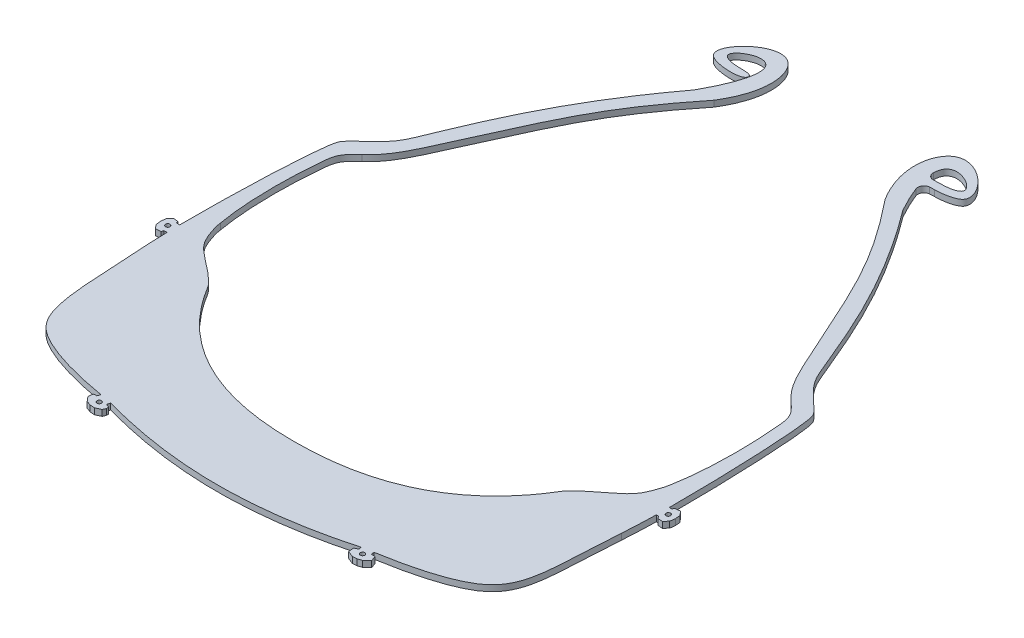
SolidWorks part; units mm, degrees
ref_plane "Front Plane" through (0, 0, 0) normal (0, 0, 1) x (1, 0, 0)
ref_plane "Top Plane" through (0, 0, 0) normal (0, 1, 0) x (1, 0, 0)
ref_plane "Right Plane" through (0, 0, 0) normal (1, 0, 0) x (0, 0, -1)
sketch "Sketch1" plane through (0, 0, 0) normal (0, 1, 0) x (1, 0, 0)
  line L0 (-56.7342, 4649.685) -> (-54.3432, 4649.8666)
  line L1 (-54.3432, 4649.8666) -> (-51.9673, 4650.1279)
  line L2 (-51.9673, 4650.1279) -> (-49.6128, 4650.4904)
  line L3 (-49.6128, 4650.4904) -> (-47.2873, 4650.9763)
  line L4 (-47.2873, 4650.9763) -> (-45.0028, 4651.606)
  line L5 (-45.0028, 4651.606) -> (-42.7754, 4652.393)
  line L6 (-42.7754, 4652.393) -> (-40.6236, 4653.3398)
  line L7 (-40.6236, 4653.3398) -> (-38.5569, 4654.4471)
  line L8 (-38.5569, 4654.4471) -> (-36.5628, 4655.7048)
  line L9 (-36.5628, 4655.7048) -> (-34.628, 4657.0886)
  line L10 (-34.628, 4657.0886) -> (-32.7572, 4658.5809)
  line L11 (-32.7572, 4658.5809) -> (-31.8781, 4659.3559)
  line L12 (-31.8781, 4659.3559) -> (-31.0378, 4660.1663)
  line L13 (-31.0378, 4660.1663) -> (-30.2434, 4661.0133)
  line L14 (-30.2434, 4661.0133) -> (-29.4929, 4661.8977)
  line L15 (-29.4929, 4661.8977) -> (-28.0377, 4663.8002)
  line L16 (-28.0377, 4663.8002) -> (-26.6418, 4665.7643)
  line L17 (-26.6418, 4665.7643) -> (-25.2842, 4667.7433)
  line L18 (-25.2842, 4667.7433) -> (-24.5616, 4668.7671)
  line L19 (-24.5616, 4668.7671) -> (-24.1207, 4669.3049)
  line L20 (-24.1207, 4669.3049) -> (-23.6287, 4669.8041)
  line L21 (-23.6287, 4669.8041) -> (-22.6527, 4670.6453)
  line L22 (-22.6527, 4670.6453) -> (-21.6624, 4671.4168)
  line L23 (-21.6624, 4671.4168) -> (-19.7154, 4672.8766)
  line L24 (-19.7154, 4672.8766) -> (-18.7888, 4673.6051)
  line L25 (-18.7888, 4673.6051) -> (-17.9151, 4674.3646)
  line L26 (-17.9151, 4674.3646) -> (-17.0961, 4675.1711)
  line L27 (-17.0961, 4675.1711) -> (-16.3332, 4676.0235)
  line L28 (-16.3332, 4676.0235) -> (-14.888, 4677.8872)
  line L29 (-14.888, 4677.8872) -> (-14.2651, 4678.8282)
  line L30 (-14.2651, 4678.8282) -> (-13.7395, 4679.8092)
  line L31 (-13.7395, 4679.8092) -> (-13.3157, 4680.8364)
  line L32 (-13.3157, 4680.8364) -> (-12.9921, 4681.9053)
  line L33 (-12.9921, 4681.9053) -> (-12.765, 4683.0137)
  line L34 (-12.765, 4683.0137) -> (-12.6116, 4684.156)
  line L35 (-12.6116, 4684.156) -> (-12.4221, 4686.5439)
  line L36 (-12.4221, 4686.5439) -> (-12.3049, 4688.9547)
  line L37 (-12.3049, 4688.9547) -> (-12.23, 4691.3606)
  line L38 (-12.23, 4691.3606) -> (-12.2173, 4693.7469)
  line L39 (-12.2173, 4693.7469) -> (-12.2979, 4696.128)
  line L40 (-12.2979, 4696.128) -> (-12.4621, 4698.525)
  line L41 (-12.4621, 4698.525) -> (-12.9016, 4703.3562)
  line L42 (-12.9016, 4703.3562) -> (-13.1725, 4705.7323)
  line L43 (-13.1725, 4705.7323) -> (-13.359, 4706.8497)
  line L44 (-13.359, 4706.8497) -> (-13.6464, 4707.8976)
  line L45 (-13.6464, 4707.8976) -> (-13.8331, 4708.3435)
  line L46 (-13.8331, 4708.3435) -> (-14.0727, 4708.7863)
  line L47 (-14.0727, 4708.7863) -> (-14.3603, 4709.2104)
  line L48 (-14.3603, 4709.2104) -> (-14.6922, 4709.6118)
  line L49 (-14.6922, 4709.6118) -> (-15.5352, 4710.4427)
  line L50 (-15.5352, 4710.4427) -> (-16.4733, 4711.2489)
  line L51 (-16.4733, 4711.2489) -> (-18.3969, 4712.8768)
  line L52 (-18.3969, 4712.8768) -> (-19.3317, 4713.7593)
  line L53 (-19.3317, 4713.7593) -> (-19.7964, 4714.2738)
  line L54 (-19.7964, 4714.2738) -> (-20.226, 4714.8564)
  line L55 (-20.226, 4714.8564) -> (-20.8491, 4716.0227)
  line L56 (-20.8491, 4716.0227) -> (-21.3607, 4717.2182)
  line L57 (-21.3607, 4717.2182) -> (-22.2565, 4719.6128)
  line L58 (-22.2565, 4719.6128) -> (-23.9365, 4724.4003)
  line L59 (-23.9365, 4724.4003) -> (-24.8142, 4726.6925)
  line L60 (-24.8142, 4726.6925) -> (-25.7235, 4728.951)
  line L61 (-25.7235, 4728.951) -> (-29.4192, 4737.978)
  line L62 (-29.4192, 4737.978) -> (-31.3112, 4742.476)
  line L63 (-31.3112, 4742.476) -> (-32.3108, 4744.6883)
  line L64 (-32.3108, 4744.6883) -> (-33.3653, 4746.8748)
  line L65 (-33.3653, 4746.8748) -> (-34.484, 4749.0197)
  line L66 (-34.484, 4749.0197) -> (-35.6822, 4751.1089)
  line L67 (-35.6822, 4751.1089) -> (-36.9697, 4753.1376)
  line L68 (-36.9697, 4753.1376) -> (-38.335, 4755.1176)
  line L69 (-38.335, 4755.1176) -> (-39.7566, 4757.0561)
  line L70 (-39.7566, 4757.0561) -> (-41.2239, 4758.9538)
  line L71 (-41.2239, 4758.9538) -> (-44.2837, 4762.6862)
  line L72 (-44.2837, 4762.6862) -> (-45.0093, 4763.5782)
  line L73 (-45.7102, 4766.0333) -> (-45.6003, 4766.895)
  line L74 (-44.3387, 4767.2717) -> (-41.5099, 4763.9631)
  line L75 (-41.5099, 4763.9631) -> (-39.7615, 4761.7893)
  line L76 (-39.7615, 4761.7893) -> (-36.1552, 4757.1077)
  line L77 (-36.1552, 4757.1077) -> (-34.4224, 4754.6956)
  line L78 (-34.4224, 4754.6956) -> (-32.818, 4752.1875)
  line L79 (-32.818, 4752.1875) -> (-31.4001, 4749.5854)
  line L80 (-31.4001, 4749.5854) -> (-30.1172, 4746.945)
  line L81 (-30.1172, 4746.945) -> (-27.7453, 4741.6402)
  line L82 (-27.7453, 4741.6402) -> (-25.4835, 4736.2816)
  line L83 (-25.4835, 4736.2816) -> (-23.2904, 4730.8724)
  line L84 (-23.2904, 4730.8724) -> (-21.1708, 4725.4153)
  line L85 (-21.1708, 4725.4153) -> (-19.1018, 4719.943)
  line L86 (-19.1018, 4719.943) -> (-18.1004, 4717.2034)
  line L87 (-18.1004, 4717.2034) -> (-17.875, 4716.5966)
  line L88 (-17.875, 4716.5966) -> (-17.6236, 4716.1359)
  line L89 (-17.6236, 4716.1359) -> (-17.2675, 4715.7336)
  line L90 (-17.2675, 4715.7336) -> (-16.7845, 4715.2999)
  line L91 (-16.7845, 4715.2999) -> (-14.566, 4713.4273)
  line L92 (-14.566, 4713.4273) -> (-13.4359, 4712.453)
  line L93 (-13.4359, 4712.453) -> (-12.2875, 4711.3506)
  line L94 (-12.2875, 4711.3506) -> (-11.7288, 4710.5494)
  line L95 (-11.7288, 4710.5494) -> (-11.4049, 4709.6505)
  line L96 (-11.4049, 4709.6505) -> (-11.1035, 4708.0976)
  line L97 (-11.1035, 4708.0976) -> (-10.7039, 4705.1867)
  line L98 (-10.7039, 4705.1867) -> (-10.3782, 4702.2301)
  line L99 (-10.3782, 4702.2301) -> (-10.1381, 4699.312)
  line L100 (-10.1381, 4699.312) -> (-9.9526, 4696.4059)
  line L101 (-9.9526, 4696.4059) -> (-9.8234, 4693.4642)
  line L102 (-9.8234, 4693.4642) -> (-9.7818, 4690.5097)
  line L103 (-9.7818, 4690.5097) -> (-9.8395, 4687.5651)
  line L104 (-9.8395, 4687.5651) -> (-10.1467, 4681.8499)
  line L105 (-10.2187, 4680.4106) -> (-10.5778, 4674.8324)
  line L106 (-10.5778, 4674.8324) -> (-10.9255, 4669.1921)
  line L107 (-10.9255, 4669.1921) -> (-11.1085, 4666.3239)
  line L108 (-11.1085, 4666.3239) -> (-11.3672, 4663.3976)
  line L109 (-11.3672, 4663.3976) -> (-11.5954, 4661.8877)
  line L110 (-11.5954, 4661.8877) -> (-11.9481, 4660.3817)
  line L111 (-11.9481, 4660.3817) -> (-12.469, 4658.9063)
  line L112 (-12.469, 4658.9063) -> (-13.1768, 4657.5086)
  line L113 (-13.1768, 4657.5086) -> (-14.0475, 4656.2056)
  line L114 (-14.0475, 4656.2056) -> (-15.0678, 4655.0233)
  line L115 (-15.0678, 4655.0233) -> (-15.6664, 4654.4674)
  line L116 (-15.6664, 4654.4674) -> (-16.3022, 4653.9611)
  line L117 (-16.3022, 4653.9611) -> (-17.6055, 4653.1269)
  line L118 (-17.6055, 4653.1269) -> (-18.9712, 4652.4383)
  line L119 (-18.9712, 4652.4383) -> (-20.3502, 4651.8561)
  line L120 (-20.3502, 4651.8561) -> (-21.7405, 4651.3486)
  line L121 (-21.7405, 4651.3486) -> (-23.1491, 4650.8937)
  line L122 (-23.1491, 4650.8937) -> (-25.9685, 4650.1281)
  line L123 (-25.9685, 4650.1281) -> (-28.8127, 4649.495)
  line L124 (-28.8127, 4649.495) -> (-34.3611, 4648.4388)
  line L125 (-35.7786, 4648.1905) -> (-42.1243, 4647.1501)
  line L126 (-42.1243, 4647.1501) -> (-45.3893, 4646.7207)
  line L127 (-45.3893, 4646.7207) -> (-48.6635, 4646.3827)
  line L128 (-48.6635, 4646.3827) -> (-55.1892, 4645.922)
  line L129 (-55.1892, 4645.922) -> (-61.7354, 4645.5886)
  line L130 (-61.7354, 4645.5886) -> (-63.9666, 4645.5453)
  line L131 (-63.9667, 4649.4865) -> (-59.1315, 4649.5688)
  line L132 (-59.1315, 4649.5688) -> (-56.7342, 4649.685)
  line L133 (-9.7721, 4681.8294) -> (-9.752, 4682.186)
  line L134 (-9.752, 4682.186) -> (-9.3693, 4682.5229)
  line L135 (-9.3693, 4682.5229) -> (-8.649, 4682.4768)
  line L136 (-8.649, 4682.4768) -> (-7.9775, 4681.713)
  line L137 (-7.9775, 4681.713) -> (-8.2411, 4680.2884)
  line L138 (-8.2411, 4680.2884) -> (-9.0059, 4679.6162)
  line L139 (-9.0059, 4679.6162) -> (-9.5491, 4679.6473)
  line L140 (-9.5491, 4679.6473) -> (-9.8867, 4680.0303)
  line L141 (-9.8867, 4680.0303) -> (-9.8664, 4680.3889)
  line L142 (-9.7721, 4681.8294) -> (-9.752, 4682.186)
  line L151 (-34.2991, 4648.0806) -> (-33.9447, 4648.1421)
  line L152 (-33.9447, 4648.1421) -> (-33.5285, 4647.8485)
  line L153 (-33.5285, 4647.8485) -> (-33.4056, 4647.1395)
  line L154 (-33.4056, 4647.1395) -> (-33.9931, 4646.3074)
  line L155 (-33.9931, 4646.3074) -> (-35.4108, 4646.0612)
  line L156 (-35.4108, 4646.0612) -> (-36.2441, 4646.6493)
  line L157 (-36.2441, 4646.6493) -> (-36.3669, 4647.358)
  line L158 (-36.3669, 4647.358) -> (-36.0733, 4647.7743)
  line L159 (-36.0733, 4647.7743) -> (-35.7187, 4647.8357)
  line L160 (-10.1467, 4681.8499) -> (-9.7721, 4681.8294)
  line L161 (-34.3611, 4648.4388) -> (-34.2991, 4648.0806)
  line L162 (-35.7786, 4648.1905) -> (-35.7187, 4647.8357)
  line L163 (-9.8664, 4680.3889) -> (-10.2187, 4680.4106)
  line L165 (-118.1813, 4682.186) -> (-118.5641, 4682.5226)
  line L166 (-118.5641, 4682.5226) -> (-119.2843, 4682.4768)
  line L167 (-119.2843, 4682.4768) -> (-119.9558, 4681.7128)
  line L168 (-119.9558, 4681.7128) -> (-119.8643, 4680.2786)
  line L169 (-119.8643, 4680.2786) -> (-119.0995, 4679.6064)
  line L170 (-119.0995, 4679.6064) -> (-118.3843, 4679.6471)
  line L171 (-118.3843, 4679.6471) -> (-118.0466, 4680.0303)
  line L172 (-118.0466, 4680.0303) -> (-118.0672, 4680.3889)
  line L173 (-118.0672, 4680.3889) -> (-117.7148, 4680.4103)
  line L174 (-117.7148, 4680.4103) -> (-117.3555, 4674.8322)
  line L175 (-117.3555, 4674.8322) -> (-117.0078, 4669.1921)
  line L176 (-117.0078, 4669.1921) -> (-116.8249, 4666.3237)
  line L177 (-116.8249, 4666.3237) -> (-116.566, 4663.3974)
  line L178 (-116.566, 4663.3974) -> (-116.3378, 4661.8875)
  line L179 (-116.3378, 4661.8875) -> (-115.9851, 4660.3817)
  line L180 (-115.9851, 4660.3817) -> (-115.4645, 4658.906)
  line L181 (-115.4645, 4658.906) -> (-114.7563, 4657.5086)
  line L182 (-114.7563, 4657.5086) -> (-113.8857, 4656.2053)
  line L183 (-113.8857, 4656.2053) -> (-112.8656, 4655.0233)
  line L184 (-112.8656, 4655.0233) -> (-112.2669, 4654.4674)
  line L185 (-112.2669, 4654.4674) -> (-111.6311, 4653.9608)
  line L186 (-111.6311, 4653.9608) -> (-110.328, 4653.1269)
  line L187 (-110.328, 4653.1269) -> (-108.9621, 4652.4383)
  line L188 (-108.9621, 4652.4383) -> (-107.5832, 4651.8561)
  line L189 (-107.5832, 4651.8561) -> (-106.1928, 4651.3484)
  line L190 (-106.1928, 4651.3484) -> (-104.7844, 4650.8937)
  line L191 (-104.7844, 4650.8937) -> (-101.9649, 4650.1279)
  line L192 (-101.9649, 4650.1279) -> (-99.1205, 4649.4948)
  line L193 (-99.1205, 4649.4948) -> (-93.5721, 4648.4388)
  line L194 (-93.5721, 4648.4388) -> (-93.6341, 4648.0806)
  line L195 (-93.6341, 4648.0806) -> (-93.9885, 4648.1421)
  line L196 (-93.9885, 4648.1421) -> (-94.4046, 4647.8485)
  line L197 (-94.4046, 4647.8485) -> (-94.5276, 4647.1392)
  line L198 (-94.5276, 4647.1392) -> (-93.9404, 4646.3074)
  line L199 (-93.9404, 4646.3074) -> (-92.5223, 4646.0612)
  line L200 (-92.5223, 4646.0612) -> (-91.6891, 4646.6493)
  line L201 (-91.6891, 4646.6493) -> (-91.5662, 4647.358)
  line L202 (-91.5662, 4647.358) -> (-91.8598, 4647.7743)
  line L203 (-91.8598, 4647.7743) -> (-92.2145, 4647.8357)
  line L204 (-92.1546, 4648.1905) -> (-92.2145, 4647.8357)
  line L205 (-92.1546, 4648.1905) -> (-85.8089, 4647.1501)
  line L206 (-85.8089, 4647.1501) -> (-82.5441, 4646.7204)
  line L207 (-82.5441, 4646.7204) -> (-79.2698, 4646.3827)
  line L208 (-79.2698, 4646.3827) -> (-72.7439, 4645.922)
  line L209 (-72.7439, 4645.922) -> (-66.1978, 4645.5886)
  line L210 (-66.1978, 4645.5886) -> (-63.9666, 4645.5453)
  line L211 (-63.9667, 4649.4865) -> (-68.8018, 4649.5688)
  line L212 (-68.8018, 4649.5688) -> (-71.1991, 4649.685)
  line L213 (-71.1991, 4649.685) -> (-73.5901, 4649.8666)
  line L214 (-73.5901, 4649.8666) -> (-75.9659, 4650.1279)
  line L215 (-75.9659, 4650.1279) -> (-78.3204, 4650.4904)
  line L216 (-78.3204, 4650.4904) -> (-80.646, 4650.976)
  line L217 (-80.646, 4650.976) -> (-82.9304, 4651.606)
  line L218 (-82.9304, 4651.606) -> (-85.1578, 4652.393)
  line L219 (-85.1578, 4652.393) -> (-87.3097, 4653.3398)
  line L220 (-87.3097, 4653.3398) -> (-89.3762, 4654.4469)
  line L221 (-89.3762, 4654.4469) -> (-91.3704, 4655.7045)
  line L222 (-91.3704, 4655.7045) -> (-93.3054, 4657.0883)
  line L223 (-93.3054, 4657.0883) -> (-95.1761, 4658.5809)
  line L224 (-95.1761, 4658.5809) -> (-96.0551, 4659.3559)
  line L225 (-96.0551, 4659.3559) -> (-96.8955, 4660.1661)
  line L226 (-96.8955, 4660.1661) -> (-97.6899, 4661.013)
  line L227 (-97.6899, 4661.013) -> (-98.4405, 4661.8974)
  line L228 (-98.4405, 4661.8974) -> (-99.8956, 4663.8003)
  line L229 (-99.8956, 4663.8003) -> (-101.2917, 4665.7643)
  line L230 (-101.2917, 4665.7643) -> (-102.649, 4667.7433)
  line L231 (-102.649, 4667.7433) -> (-103.3717, 4668.7671)
  line L232 (-103.3717, 4668.7671) -> (-103.8126, 4669.3049)
  line L233 (-103.8126, 4669.3049) -> (-104.3045, 4669.8038)
  line L234 (-104.3045, 4669.8038) -> (-105.2805, 4670.645)
  line L235 (-105.2805, 4670.645) -> (-106.2711, 4671.4168)
  line L236 (-106.2711, 4671.4168) -> (-108.218, 4672.8766)
  line L237 (-108.218, 4672.8766) -> (-109.1446, 4673.6051)
  line L238 (-109.1446, 4673.6051) -> (-110.0184, 4674.3646)
  line L239 (-110.0184, 4674.3646) -> (-110.8371, 4675.1711)
  line L240 (-110.8371, 4675.1711) -> (-111.6001, 4676.0232)
  line L241 (-111.6001, 4676.0232) -> (-113.0454, 4677.8872)
  line L242 (-113.0454, 4677.8872) -> (-113.6683, 4678.8282)
  line L243 (-113.6683, 4678.8282) -> (-114.1938, 4679.8092)
  line L244 (-114.1938, 4679.8092) -> (-114.6176, 4680.8364)
  line L245 (-114.6176, 4680.8364) -> (-114.9413, 4681.905)
  line L246 (-114.9413, 4681.905) -> (-115.1684, 4683.0135)
  line L247 (-115.1684, 4683.0135) -> (-115.3218, 4684.156)
  line L248 (-115.3218, 4684.156) -> (-115.5115, 4686.5436)
  line L249 (-115.5115, 4686.5436) -> (-115.6283, 4688.9545)
  line L250 (-115.6283, 4688.9545) -> (-115.7033, 4691.3606)
  line L251 (-115.7033, 4691.3606) -> (-115.7161, 4693.7466)
  line L252 (-115.7161, 4693.7466) -> (-115.6355, 4696.1278)
  line L253 (-115.6355, 4696.1278) -> (-115.4714, 4698.525)
  line L254 (-115.4714, 4698.525) -> (-115.0316, 4703.3562)
  line L255 (-115.0316, 4703.3562) -> (-114.7608, 4705.732)
  line L256 (-114.7608, 4705.732) -> (-114.5743, 4706.8497)
  line L257 (-114.5743, 4706.8497) -> (-114.287, 4707.8977)
  line L258 (-114.287, 4707.8977) -> (-114.1002, 4708.3435)
  line L259 (-114.1002, 4708.3435) -> (-113.8608, 4708.7862)
  line L260 (-113.8608, 4708.7862) -> (-113.5731, 4709.2103)
  line L261 (-113.5731, 4709.2103) -> (-113.2411, 4709.6117)
  line L262 (-113.2411, 4709.6117) -> (-112.3981, 4710.4425)
  line L263 (-112.3981, 4710.4425) -> (-111.4599, 4711.2487)
  line L264 (-111.4599, 4711.2487) -> (-109.5364, 4712.8767)
  line L265 (-109.5364, 4712.8767) -> (-108.602, 4713.7592)
  line L266 (-108.602, 4713.7592) -> (-108.1369, 4714.2737)
  line L267 (-108.1369, 4714.2737) -> (-107.7072, 4714.8564)
  line L268 (-107.7072, 4714.8564) -> (-107.0842, 4716.0225)
  line L269 (-107.0842, 4716.0225) -> (-106.5727, 4717.2181)
  line L270 (-106.5727, 4717.2181) -> (-105.6769, 4719.6127)
  line L271 (-105.6769, 4719.6127) -> (-103.9969, 4724.4001)
  line L272 (-103.9969, 4724.4001) -> (-103.1193, 4726.6924)
  line L273 (-103.1193, 4726.6924) -> (-102.2099, 4728.9509)
  line L274 (-102.2099, 4728.9509) -> (-98.5143, 4737.9778)
  line L275 (-98.5143, 4737.9778) -> (-96.6221, 4742.4757)
  line L276 (-96.6221, 4742.4757) -> (-95.6227, 4744.6884)
  line L277 (-95.6227, 4744.6884) -> (-94.5682, 4746.8748)
  line L278 (-94.5682, 4746.8748) -> (-93.4493, 4749.0197)
  line L279 (-93.4493, 4749.0197) -> (-92.2515, 4751.1088)
  line L280 (-92.2515, 4751.1088) -> (-90.9637, 4753.1374)
  line L281 (-90.9637, 4753.1374) -> (-89.5985, 4755.1174)
  line L282 (-89.5985, 4755.1174) -> (-88.177, 4757.0561)
  line L283 (-88.177, 4757.0561) -> (-86.7094, 4758.9538)
  line L284 (-86.7094, 4758.9538) -> (-83.65, 4762.6862)
  line L285 (-83.65, 4762.6862) -> (-82.924, 4763.5782)
  line L286 (-82.2232, 4766.0334) -> (-82.3333, 4766.8949)
  line L287 (-83.5948, 4767.2716) -> (-86.4235, 4763.963)
  line L288 (-86.4235, 4763.963) -> (-88.172, 4761.7894)
  line L289 (-88.172, 4761.7894) -> (-91.7784, 4757.1074)
  line L290 (-91.7784, 4757.1074) -> (-93.5112, 4754.6958)
  line L291 (-93.5112, 4754.6958) -> (-95.1154, 4752.1875)
  line L292 (-95.1154, 4752.1875) -> (-96.5333, 4749.5852)
  line L293 (-96.5333, 4749.5852) -> (-97.8162, 4746.9449)
  line L294 (-97.8162, 4746.9449) -> (-100.1881, 4741.6403)
  line L295 (-100.1881, 4741.6403) -> (-102.4501, 4736.2814)
  line L296 (-102.4501, 4736.2814) -> (-104.6429, 4730.8726)
  line L297 (-104.6429, 4730.8726) -> (-106.7626, 4725.415)
  line L298 (-106.7626, 4725.415) -> (-108.8314, 4719.9429)
  line L299 (-108.8314, 4719.9429) -> (-109.8329, 4717.2035)
  line L300 (-109.8329, 4717.2035) -> (-110.0583, 4716.5964)
  line L301 (-110.0583, 4716.5964) -> (-110.3097, 4716.1357)
  line L302 (-110.3097, 4716.1357) -> (-110.6661, 4715.7335)
  line L303 (-110.6661, 4715.7335) -> (-111.1489, 4715.2998)
  line L304 (-111.1489, 4715.2998) -> (-113.3676, 4713.4272)
  line L305 (-113.3676, 4713.4272) -> (-114.4976, 4712.4528)
  line L306 (-114.4976, 4712.4528) -> (-115.646, 4711.3505)
  line L307 (-115.646, 4711.3505) -> (-116.2044, 4710.5493)
  line L308 (-116.2044, 4710.5493) -> (-116.5286, 4709.6504)
  line L309 (-116.5286, 4709.6504) -> (-116.8298, 4708.0975)
  line L310 (-116.8298, 4708.0975) -> (-117.2296, 4705.1868)
  line L311 (-117.2296, 4705.1868) -> (-117.5553, 4702.2301)
  line L312 (-117.5553, 4702.2301) -> (-117.7952, 4699.312)
  line L313 (-117.7952, 4699.312) -> (-117.981, 4696.4059)
  line L314 (-117.981, 4696.4059) -> (-118.11, 4693.4642)
  line L315 (-118.11, 4693.4642) -> (-118.1516, 4690.5097)
  line L316 (-118.1516, 4690.5097) -> (-118.0939, 4687.5649)
  line L317 (-118.0939, 4687.5649) -> (-117.7865, 4681.8497)
  line L318 (-117.7865, 4681.8497) -> (-118.1612, 4681.8294)
  line L319 (-118.1612, 4681.8294) -> (-118.1813, 4682.186)
  spline S0 degree 3 poles (-45.7102, 4766.0333) (-45.8224, 4765.1537) (-45.5692, 4764.2663) (-45.0093, 4763.5782) knots 0 0 0 0 1 1 1 1
  spline S1 degree 3 poles (-44.3387, 4767.2717) (-44.5973, 4767.574) (-45.0517, 4767.6095) (-45.3539, 4767.351) knots 0 0 0 0 1 1 1 1
  spline S2 degree 3 poles (-45.3539, 4767.351) (-45.4898, 4767.2349) (-45.5777, 4767.0723) (-45.6003, 4766.895) knots 0 0 0 0 1 1 1 1
  spline S3 degree 3 poles (-82.924, 4763.5782) (-82.3642, 4764.2661) (-82.111, 4765.1536) (-82.2232, 4766.0334) knots 0 0 0 0 1 1 1 1
  spline S4 degree 3 poles (-82.3333, 4766.8949) (-82.3835, 4767.2894) (-82.7441, 4767.5683) (-83.1386, 4767.518) knots 0 0 0 0 1 1 1 1
  spline S5 degree 3 poles (-83.1386, 4767.518) (-83.3159, 4767.4954) (-83.4785, 4767.4075) (-83.5948, 4767.2716) knots 0 0 0 0 1 1 1 1
sketch "Sketch2" plane through (0, 0, 0) normal (0, 1, 0) x (1, 0, 0)
  line L0 (-63.9234, 4631.4262) -> (-63.9234, 4609.4594) construction
  line L25 (-22.4985, 4637.3551) -> (-18.9434, 4638.0357) construction
  line L26 (-20.7209, 4637.6954) -> (-20.3316, 4635.6618) construction
  line L31 (-16.9423, 4635.297) -> (-18.5347, 4633.796)
  line L32 (-20.3316, 4635.6618) -> (-19.8467, 4633.1287) construction
  line L33 (-18.5347, 4633.796) -> (-19.8873, 4633.3404)
  line L34 (-21.3125, 4633.2642) -> (-19.8873, 4633.3404)
  line L35 (-23.3466, 4634.071) -> (-21.3125, 4633.2642)
  line L40 (-104.4735, 4635.7404) -> (-104.4735, 4634.9567)
  line L41 (-104.4735, 4634.9567) -> (-104.8805, 4633.998)
  line L42 (-104.8805, 4633.998) -> (-106.6203, 4633.1744)
  line L43 (-106.6203, 4633.1744) -> (-108.2043, 4633.2927)
  line L44 (-109.6975, 4633.8343) -> (-108.2043, 4633.2927)
  line L45 (-110.9466, 4635.2989) -> (-109.6975, 4633.8343)
  line L46 (-110.9246, 4636.3402) -> (-110.9466, 4635.2989)
  line L47 (-110.6737, 4637.0191) -> (-110.9246, 4636.3402)
  line L49 (-146.8202, 4697.6298) -> (-149.3915, 4697.5949) construction
  line L50 (16.9036, 4697.658) -> (18.9735, 4697.6298) construction
  line L54 (20.0716, 4700.6062) -> (21.1812, 4699.2558)
  line L55 (18.9735, 4697.6298) -> (21.5448, 4697.5949) construction
  line L56 (21.1812, 4699.2558) -> (21.376, 4697.5972)
  line L57 (21.1362, 4695.9445) -> (21.376, 4697.5972)
  line L58 (19.9903, 4694.6247) -> (21.1362, 4695.9445)
  line L62 (-144.7504, 4697.658) -> (-146.8202, 4697.6298) construction
  line L67 (-148.983, 4695.9445) -> (-149.2228, 4697.5972)
  line L68 (-149.028, 4699.2558) -> (-149.2228, 4697.5972)
  line L69 (-147.9184, 4700.6062) -> (-149.028, 4699.2558)
  line L73 (18.4279, 4700.4703) -> (20.0716, 4700.6062)
  line L74 (18.3509, 4694.8052) -> (19.9903, 4694.6247)
  line L75 (-23.4805, 4635.8657) -> (-23.3466, 4634.071)
  line L76 (-17.4807, 4637.0143) -> (-16.9423, 4635.297)
  line L77 (-32.327, 4837.4932) -> (-33.002, 4837.4569)
  line L78 (-30.1616, 4834.8716) -> (-31.6461, 4834.7997)
  line L79 (-146.2747, 4700.4703) -> (-146.0774, 4699.7908)
  line L80 (-146.0774, 4699.7908) -> (-144.9978, 4699.7908)
  line L81 (-146.1977, 4694.8052) -> (-145.9394, 4695.5191)
  line L82 (-145.9394, 4695.5191) -> (-144.9397, 4695.5191)
  line L83 (-110.6737, 4637.0191) -> (-109.7005, 4637.0191)
  line L84 (-109.7005, 4637.0191) -> (-109.3372, 4638.0212)
  line L85 (-104.4735, 4635.7404) -> (-105.6297, 4636.1595)
  line L86 (-105.6297, 4636.1595) -> (-105.3482, 4637.2394)
  line L87 (-23.4805, 4635.8657) -> (-22.2692, 4636.4725)
  line L88 (-22.2692, 4636.4725) -> (-22.4985, 4637.3551)
  line L89 (-17.4807, 4637.0143) -> (-18.7231, 4637.0143)
  line L90 (-18.7231, 4637.0143) -> (-18.9434, 4638.0357)
  line L91 (17.093, 4695.5191) -> (17.927, 4695.5191)
  line L92 (17.927, 4695.5191) -> (18.3509, 4694.8052)
  line L93 (17.151, 4699.7908) -> (17.9273, 4699.7908)
  line L94 (17.9273, 4699.7908) -> (18.4279, 4700.4703)
  line L95 (-147.9184, 4700.6062) -> (-146.2747, 4700.4703)
  line L96 (-148.983, 4695.9445) -> (-147.9184, 4694.6247)
  line L97 (-147.9184, 4694.6247) -> (-146.1977, 4694.8052)
  circle A0 centre (28.2666, 4698.0399) radius 0.5
  circle A1 centre (-20.3316, 4635.6618) radius 0.75
  circle A2 centre (-107.5151, 4635.6618) radius 0.75
  circle A4 centre (18.9735, 4697.6298) radius 0.75
  circle A5 centre (-146.8202, 4697.6298) radius 0.75
  arc A6 (-33.4175, 4832.0881) -> (-31.6461, 4834.7997) centre (-31.5493, 4832.802) cw
  arc A7 (-35.1093, 4839.4705) -> (-33.002, 4837.4569) centre (-33.1094, 4839.454) ccw
  spline S0 degree 3 poles (-105.3482, 4637.2394) (-91.774, 4633.4496) (-63.9165, 4629.3481) (-36.075, 4633.5591) (-22.4985, 4637.3551) knots 0.018742 0.018742 0.018742 0.018742 0.500293 0.981945 0.981945 0.981945 0.981945
  spline S1 degree 3 poles (-18.9434, 4638.0357) (-9.0248, 4639.6859) (4.6467, 4643.0604) (16.372, 4654.3944) (15.2524, 4666.3346) (16.6172, 4684.5147) knots 0.018902 0.018902 0.018902 0.018902 0.394122 0.490995 0.987629 0.987629 0.987629 0.987629
  spline S2 degree 3 poles (16.6172, 4684.5147) (16.7593, 4687.5885) (17.0552, 4691.3248) (17.093, 4695.5191) knots 0.004735 0.004735 0.004735 0.004735 0.035162 0.035162 0.035162 0.035162
  spline S3 degree 3 poles (17.151, 4699.7908) (17.187, 4718.7532) (15.9463, 4748.1487) (12.9962, 4752.2098) (5.5902, 4758.1386) (-2.0807, 4776.0799) (-10.7985, 4798.9266) (-29.4127, 4823.6906) knots 0.04445 0.04445 0.04445 0.04445 0.175223 0.204985 0.326837 0.407861 1 1 1 1
  spline S4 degree 2 poles (-63.9234, 4656.5726) (-23.3221, 4656.4521) (-5.293, 4686.6697) knots 0 0 0 1 1 1
  spline S5 degree 3 poles (-5.293, 4686.6697) (-3.3882, 4689.5147) (5.5322, 4695.6316) (7.0158, 4697.627) (8.9185, 4699.9572) (10.6489, 4704.6448) (10.9298, 4707.0618) knots 0 0 0 0 0.517385 0.711984 0.762678 1 1 1 1
  spline S6 degree 3 poles (10.9298, 4707.0618) (12.5257, 4715.666) (12.951, 4730.9053) (11.2091, 4746.2487) (8.6834, 4748.7091) (7.186, 4750.111) knots 0 0 0 0 0.7977 0.8977 1 1 1 1
  spline S7 degree 3 poles (7.186, 4750.111) (2.646, 4753.9033) (-14.4766, 4791.3077) (-18.8927, 4803.2089) (-35.5809, 4824.0367) knots 0 0 0 0 0.147118 0.925748 0.925748 0.925748 0.925748
  spline S8 degree 3 poles (-29.4127, 4823.6906) (-30.3085, 4825.3104) (-31.8576, 4828.323) (-32.9643, 4830.902) (-33.4175, 4832.0881) knots 0 0 0 0 0.008449 0.016898 0.016898 0.016898 0.016898
  spline S9 degree 3 poles (-98.4913, 4823.6906) (-93.3668, 4832.9571) (-89.9418, 4849.3789) (-105.7855, 4840.5182) (-99.8769, 4837.047) (-93.6388, 4838.0423) (-92.6342, 4834.1705) (-104.6444, 4834.7511) (-107.7562, 4841.8445) (-89.7196, 4857.0798) (-85.226, 4835.3422) (-92.2658, 4824.0367) knots 0 0 0 0 0.048335 0.142928 0.16216 0.231927 0.259382 0.409256 0.461524 0.763332 1 1 1 1
  spline S10 degree 3 poles (-135.0327, 4750.111) (-130.4927, 4753.9033) (-113.3702, 4791.3077) (-108.954, 4803.2089) (-92.2658, 4824.0367) knots 0 0 0 0 0.147118 0.925748 0.925748 0.925748 0.925748
  spline S11 degree 3 poles (-138.7766, 4707.0618) (-140.3724, 4715.666) (-140.7978, 4730.9053) (-139.0558, 4746.2487) (-136.5302, 4748.7091) (-135.0327, 4750.111) knots 0 0 0 0 0.7977 0.8977 1 1 1 1
  spline S12 degree 3 poles (-122.5537, 4686.6697) (-124.4586, 4689.5147) (-133.3789, 4695.6316) (-134.8625, 4697.627) (-136.7653, 4699.9572) (-138.4957, 4704.6448) (-138.7766, 4707.0618) knots 0 0 0 0 0.517385 0.711984 0.762678 1 1 1 1
  spline S13 degree 2 poles (-63.9234, 4656.5726) (-104.5246, 4656.4521) (-122.5537, 4686.6697) knots 0 0 0 1 1 1
  spline S14 degree 3 poles (-144.7494, 4689.4807) (-144.8339, 4691.3079) (-144.8968, 4693.3424) (-144.9397, 4695.5191) knots 0.004735 0.004735 0.004735 0.004735 0.022822 0.022822 0.022822 0.022822
  spline S15 degree 3 poles (-109.3372, 4638.0212) (-119.1435, 4639.6853) (-132.6028, 4643.2518) (-144.26, 4654.2895) (-143.3596, 4671.4378) (-144.7494, 4689.4807) knots 0.024856 0.024856 0.024856 0.024856 0.394717 0.491493 0.992616 0.992616 0.992616 0.992616
  spline S16 degree 3 poles (-35.1093, 4839.4705) (-35.1035, 4840.1756) (-34.1088, 4847.2234) (-22.3618, 4840.6918) (-27.115, 4837.4512) (-30.5323, 4837.5897) (-32.327, 4837.4932) knots 0.039445 0.039445 0.039445 0.039445 0.048335 0.142928 0.159173 0.210778 0.210778 0.210778 0.210778
  spline S17 degree 3 poles (-30.1616, 4834.8716) (-27.3768, 4834.8692) (-22.6149, 4835.8303) (-20.678, 4842.0792) (-38.1282, 4857.0774) (-42.6207, 4835.3422) (-35.5809, 4824.0367) knots 0.329046 0.329046 0.329046 0.329046 0.418095 0.461524 0.763332 1 1 1 1
  spline S18 degree 3 poles (-144.9978, 4699.7908) (-145.1407, 4717.9008) (-143.9805, 4747.7814) (-140.9459, 4752.3436) (-133.5186, 4758.0896) (-125.8343, 4776.2877) (-117.1055, 4798.9266) (-98.4913, 4823.6906) knots 0.034256 0.034256 0.034256 0.034256 0.174203 0.204985 0.326837 0.407861 1 1 1 1
  point P97 (0, 0)
  dimension "D1" = 1
  dimension "D2" = 2
extrude "Boss-Extrude2" add sketch "Sketch2" along normal blind 2 separate body
